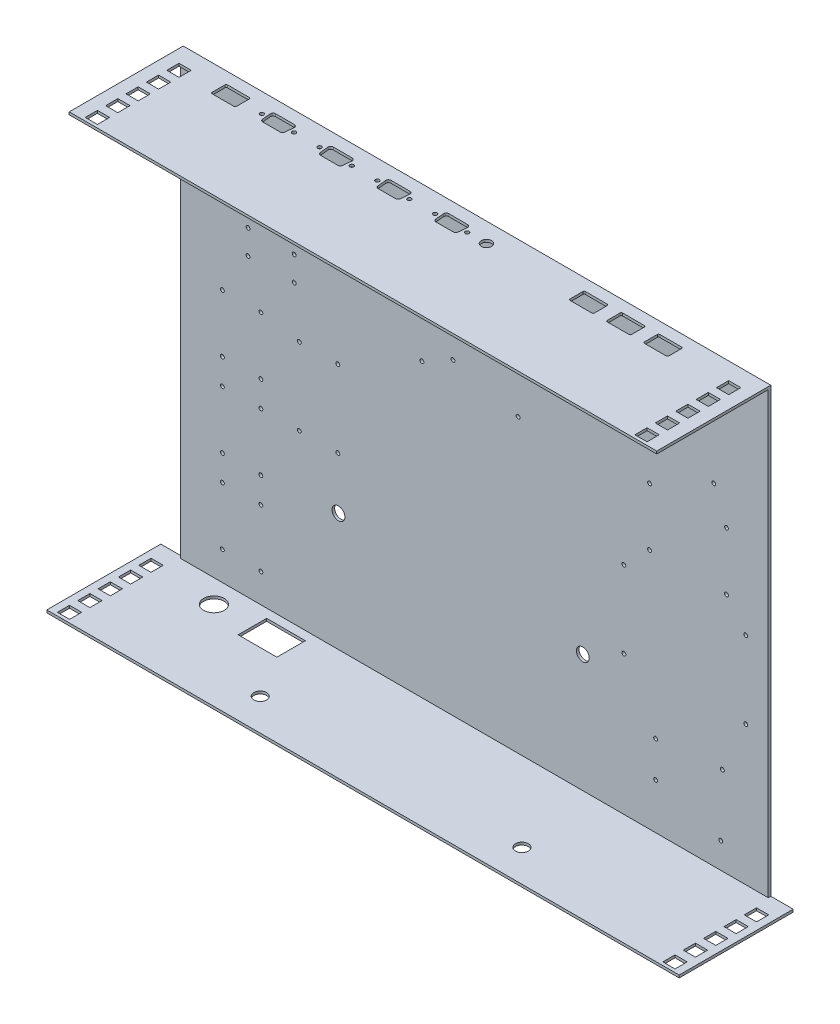
SolidWorks part; units mm, degrees
ref_plane "Front Plane" through (0, 0, 0) normal (0, 0, 1) x (1, 0, 0)
ref_plane "Top Plane" through (0, 0, 0) normal (0, 1, 0) x (1, 0, 0)
ref_plane "Right Plane" through (0, 0, 0) normal (1, 0, 0) x (0, 0, -1)
sketch "Sketch1" plane through (0, 0, 0) normal (0, 0, 1) x (1, 0, 0)
  line L13 (-229, -173.5) -> (229, -173.5)
  line L14 (-229, -173.5) -> (-229, 173.5)
  line L19 (-229, 173.5) -> (229, 173.5)
  line L20 (229, -173.5) -> (229, 173.5)
  line L21 (-229, -173.5) -> (229, 173.5) construction
  line L22 (-229, 173.5) -> (229, -173.5) construction
  point P0 (0, 0)
  dimension "D1" = 458
  dimension "D2" = 347
extrude "Boss-Extrude1" add sketch "Sketch1" along normal blind 2
sketch "Sketch4" plane through (0, -173.5, 0) normal (0, -1, 0) x (1, 0, 0)
  line L0 (-229, 2) -> (-229, 0) construction
  line L1 (-246.5, 0) -> (246.5, 0)
  line L2 (-246.5, 0) -> (-246.5, 88.9)
  line L3 (-246.5, 88.9) -> (246.5, 88.9)
  line L4 (246.5, 0) -> (246.5, 88.9)
  line L5 (229, 2) -> (229, 0) construction
  line L6 (-231.25, 88.9) -> (-231.25, 0) construction
  line L7 (-240.75, 61.02) -> (-231.25, 61.02)
  line L8 (-240.75, 86.4) -> (-231.25, 86.4)
  line L9 (-240.75, 86.4) -> (-240.75, 76.9)
  line L10 (-240.75, 76.9) -> (-231.25, 76.9)
  line L11 (-231.25, 86.4) -> (-231.25, 76.9)
  line L12 (-240.75, 70.52) -> (-240.75, 61.02)
  line L13 (-240.75, 70.52) -> (-231.25, 70.52)
  line L14 (-231.25, 70.52) -> (-231.25, 61.02)
  line L15 (-240.75, 45.14) -> (-231.25, 45.14)
  line L16 (-240.75, 54.64) -> (-240.75, 45.14)
  line L17 (-240.75, 54.64) -> (-231.25, 54.64)
  line L18 (-231.25, 54.64) -> (-231.25, 45.14)
  line L19 (-240.75, 29.26) -> (-231.25, 29.26)
  line L20 (-240.75, 38.76) -> (-240.75, 29.26)
  line L21 (-240.75, 38.76) -> (-231.25, 38.76)
  line L22 (-231.25, 38.76) -> (-231.25, 29.26)
  line L23 (-240.75, 13.38) -> (-231.25, 13.38)
  line L24 (-240.75, 22.88) -> (-240.75, 13.38)
  line L25 (-240.75, 22.88) -> (-231.25, 22.88)
  line L26 (-231.25, 22.88) -> (-231.25, 13.38)
  line L27 (0, 0) -> (0, 101.053) construction
  line L28 (231.25, 22.88) -> (231.25, 13.38)
  line L29 (240.75, 13.38) -> (231.25, 13.38)
  line L30 (240.75, 22.88) -> (240.75, 13.38)
  line L31 (240.75, 22.88) -> (231.25, 22.88)
  line L32 (231.25, 38.76) -> (231.25, 29.26)
  line L33 (240.75, 29.26) -> (231.25, 29.26)
  line L34 (240.75, 38.76) -> (240.75, 29.26)
  line L35 (240.75, 38.76) -> (231.25, 38.76)
  line L36 (240.75, 54.64) -> (240.75, 45.14)
  line L37 (231.25, 54.64) -> (231.25, 45.14)
  line L38 (240.75, 45.14) -> (231.25, 45.14)
  line L39 (240.75, 54.64) -> (231.25, 54.64)
  line L40 (231.25, 70.52) -> (231.25, 61.02)
  line L41 (240.75, 61.02) -> (231.25, 61.02)
  line L42 (240.75, 70.52) -> (231.25, 70.52)
  line L43 (240.75, 70.52) -> (240.75, 61.02)
  line L44 (231.25, 86.4) -> (231.25, 76.9)
  line L45 (240.75, 86.4) -> (231.25, 86.4)
  line L46 (240.75, 86.4) -> (240.75, 76.9)
  line L47 (240.75, 76.9) -> (231.25, 76.9)
  dimension "D1" = 17.5
  dimension "D2" = 17.5
  dimension "D3" = 88.9
  dimension "D4" = 2.25
  dimension "D5" = 9.5
  dimension "D6" = 2.5
  dimension "D7" = 9.5
  dimension "D9" = 15.88
  dimension "D8" = 5
extrude "Boss-Extrude4" add sketch "Sketch4" against normal blind 2
ref_plane "Plane1" through (0, 0, 0) normal (0, 1, 0) x (1, 0, 0)
mirror "Mirror1" about plane through (0, 0, 0) normal (0, 1, 0) of "Boss-Extrude4"
sketch "Sketch5" plane through (0, 173.5, 0) normal (0, 1, 0) x (1, 0, 0)
  line L0 (-229, 0) -> (-229, -88.9) construction
  line L1 (246.5, 0) -> (-246.5, 0) construction
  line L2 (246.5, -88.9) -> (-246.5, -88.9) construction
  line L7 (0, -55) -> (0, 55) construction
  line L11 (-229, 0) -> (-246.5, 0)
  line L12 (-229, 0) -> (-229, -88.9)
  line L13 (-229, -88.9) -> (-246.5, -88.9)
  line L14 (-246.5, 0) -> (-246.5, -88.9)
  line L15 (229, 0) -> (246.5, 0)
  line L16 (246.5, 0) -> (246.5, -88.9)
  line L17 (229, -88.9) -> (246.5, -88.9)
  line L18 (229, 0) -> (229, -88.9)
extrude "Cut-Extrude2" cut sketch "Sketch5" against normal up to next
sketch "Sketch6" plane through (0, 173.5, 0) normal (0, 1, 0) x (1, 0, 0)
  line L0 (-229, -88.9) -> (-229, 0) construction
  line L1 (-219, -13.32) -> (-209.5, -13.32)
  line L2 (-219, -13.32) -> (-219, -22.82)
  line L3 (-219, -22.82) -> (-209.5, -22.82)
  line L4 (-209.5, -13.32) -> (-209.5, -22.82)
  line L6 (-219, -29.22) -> (-219, -38.72)
  line L7 (-219, -29.22) -> (-209.5, -29.22)
  line L8 (-219, -38.72) -> (-209.5, -38.72)
  line L9 (-209.5, -29.22) -> (-209.5, -38.72)
  line L10 (-219, -45.12) -> (-219, -54.62)
  line L11 (-219, -45.12) -> (-209.5, -45.12)
  line L12 (-219, -54.62) -> (-209.5, -54.62)
  line L13 (-209.5, -45.12) -> (-209.5, -54.62)
  line L14 (-219, -61.02) -> (-219, -70.52)
  line L15 (-219, -61.02) -> (-209.5, -61.02)
  line L16 (-219, -70.52) -> (-209.5, -70.52)
  line L17 (-209.5, -61.02) -> (-209.5, -70.52)
  line L18 (-219, -76.92) -> (-219, -86.42)
  line L19 (-219, -76.92) -> (-209.5, -76.92)
  line L20 (-219, -86.42) -> (-209.5, -86.42)
  line L21 (-209.5, -76.92) -> (-209.5, -86.42)
  line L22 (0, -55) -> (0, 55) construction
  line L23 (219, -45.12) -> (209.5, -45.12)
  line L24 (219, -45.12) -> (219, -54.62)
  line L25 (209.5, -45.12) -> (209.5, -54.62)
  line L26 (219, -54.62) -> (209.5, -54.62)
  line L27 (219, -61.02) -> (209.5, -61.02)
  line L28 (209.5, -61.02) -> (209.5, -70.52)
  line L29 (219, -70.52) -> (209.5, -70.52)
  line L30 (219, -61.02) -> (219, -70.52)
  line L31 (219, -76.92) -> (219, -86.42)
  line L32 (219, -86.42) -> (209.5, -86.42)
  line L33 (209.5, -76.92) -> (209.5, -86.42)
  line L34 (219, -76.92) -> (209.5, -76.92)
  line L35 (219, -13.32) -> (219, -22.82)
  line L36 (219, -13.32) -> (209.5, -13.32)
  line L37 (209.5, -13.32) -> (209.5, -22.82)
  line L38 (219, -22.82) -> (209.5, -22.82)
  line L39 (219, -29.22) -> (219, -38.72)
  line L40 (219, -38.72) -> (209.5, -38.72)
  line L41 (209.5, -29.22) -> (209.5, -38.72)
  line L42 (219, -29.22) -> (209.5, -29.22)
  line L43 (229, -88.9) -> (-229, -88.9) construction
  dimension "D1" = 9.5
  dimension "D2" = 9.5
  dimension "D3" = 10
  dimension "D4" = 2.48
  dimension "D6" = 6.4
  dimension "D5" = 5
extrude "Cut-Extrude3" cut sketch "Sketch6" against normal up to next
sketch "Sketch9" plane through (0, 0, 2) normal (0, 0, 1) x (1, 0, 0)
  line L0 (-91, -171.5) -> (-91, 10.5) construction
  line L1 (246.5, -171.5) -> (-246.5, -171.5) construction
  line L2 (77, -171.5) -> (77, 10.5) construction
  line L3 (-229, -171.5) -> (229, -171.5) construction
  line L4 (-91, 10.5) -> (77, 10.5) construction
  line L5 (-229, 171.5) -> (-229, -171.5) construction
  circle A0 centre (-106, -79.5) radius 5
  circle A3 centre (84.5, -79.5) radius 5
  dimension "D5" = 10
  dimension "D6" = 10
  dimension "D1" = 138
  dimension "D2" = 168
  dimension "D3" = 182
  dimension "D8" = 15
  dimension "D9" = 90
  dimension "D14" = 15
  dimension "D15" = 90
extrude "Cut-Extrude4" cut sketch "Sketch9" against normal up to next
sketch "Sketch11" plane through (0, -173.5, 0) normal (0, -1, 0) x (1, 0, 0)
  line L0 (-90, 0) -> (-90, 85.1375) construction
  line L1 (-246.5, 0) -> (246.5, 0) construction
  line L2 (84, 0) -> (84, 87.0276) construction
  line L10 (-246.5, 88.9) -> (-246.5, 0) construction
  line L11 (-90, 79) -> (84, 79) construction
  circle A0 centre (-105, 64) radius 5
  circle A1 centre (99, 64) radius 5
  dimension "D4" = 10
  dimension "D5" = 10
  dimension "D1" = 174
  dimension "D2" = 156.5
  dimension "D3" = 79
  dimension "D6" = 15
  dimension "D7" = 15
  dimension "D8" = 15
  dimension "D9" = 15
extrude "Cut-Extrude5" cut sketch "Sketch11" against normal up to next
sketch "Sketch12" plane through (0, 0, 2) normal (0, 0, 1) x (1, 0, 0)
  line L0 (-229, -171.5) -> (229, -171.5) construction
  line L1 (-199, -151.5) -> (-164, -151.5)
  line L2 (-199, -151.5) -> (-199, -101.5)
  line L3 (-199, -101.5) -> (-164, -101.5)
  line L4 (-164, -151.5) -> (-164, -101.5)
  line L5 (-199, -151.5) -> (-164, -101.5) construction
  line L6 (-199, -101.5) -> (-164, -151.5) construction
  line L7 (-229, 171.5) -> (-229, -171.5) construction
  line L12 (-199, -86.5) -> (-164, -86.5)
  line L13 (-199, -86.5) -> (-199, -36.5)
  line L18 (-199, -36.5) -> (-164, -36.5)
  line L19 (-164, -86.5) -> (-164, -36.5)
  line L20 (-199, -101.5) -> (-199, 47.085) construction
  line L21 (-199, -86.5) -> (-164, -36.5) construction
  line L22 (-199, -36.5) -> (-164, -86.5) construction
  line L23 (-199, -21.5) -> (-164, -21.5)
  line L24 (-199, -21.5) -> (-199, 28.5)
  line L25 (-199, 28.5) -> (-164, 28.5)
  line L26 (-164, -21.5) -> (-164, 28.5)
  line L27 (-199, -21.5) -> (-164, 28.5) construction
  line L28 (-199, 28.5) -> (-164, -21.5) construction
  line L30 (-139, 23.5) -> (-104, 23.5)
  line L31 (-139, 23.5) -> (-139, -41.5)
  line L32 (-139, -41.5) -> (-104, -41.5)
  line L33 (-104, 23.5) -> (-104, -41.5)
  line L34 (-121.5, -41.5) -> (-121.5, 23.5) construction
  line L35 (-139, -9) -> (-104, -9) construction
  circle A0 centre (-196.5, -149) radius 1.5
  circle A1 centre (-166.5, -149) radius 1.5
  circle A2 centre (-166.5, -104) radius 1.5
  circle A3 centre (-196.5, -104) radius 1.5
  circle A12 centre (-196.5, -84) radius 1.5
  circle A13 centre (-166.5, -84) radius 1.5
  circle A14 centre (-166.5, -39) radius 1.5
  circle A15 centre (-196.5, -39) radius 1.5
  circle A16 centre (-196.5, -19) radius 1.5
  circle A17 centre (-166.5, -19) radius 1.5
  circle A18 centre (-166.5, 26) radius 1.5
  circle A19 centre (-196.5, 26) radius 1.5
  circle A20 centre (-136.5, 21) radius 1.5
  circle A21 centre (-106.5, 21) radius 1.5
  circle A22 centre (-106.5, -39) radius 1.5
  circle A23 centre (-136.5, -39) radius 1.5
  point P4 (-181.5, -126.5)
  point P21 (-181.5, -61.5)
  point P34 (-181.5, 3.5)
  point P43 (-181.5, 28.5)
  point P205 (-121.5, -9)
  dimension "D7" = 3
  dimension "D8" = 3
  dimension "D13" = 3
  dimension "D16" = 3
  dimension "D19" = 2.5
  dimension "D22" = 3
  dimension "D20" = 3
  dimension "D27" = 3
  dimension "D30" = 3
  dimension "D34" = 3
  dimension "D36" = 3
  dimension "D41" = 3
  dimension "D44" = 3
  dimension "D51" = 3
  dimension "D52" = 3
  dimension "D53" = 3
  dimension "D54" = 3
  dimension "D1" = 20
  dimension "D2" = 30
  dimension "D3" = 35
  dimension "D4" = 50
  dimension "D5" = 2.5
  dimension "D6" = 2.5
  dimension "D9" = 2.5
  dimension "D10" = 2.5
  dimension "D11" = 2.5
  dimension "D12" = 2.5
  dimension "D14" = 2.5
  dimension "D15" = 2.5
  dimension "D17" = 35
  dimension "D18" = 50
  dimension "D21" = 2.5
  dimension "D23" = 2.5
  dimension "D24" = 2.5
  dimension "D25" = 2.5
  dimension "D26" = 2.5
  dimension "D28" = 2.5
  dimension "D29" = 2.5
  dimension "D31" = 35
  dimension "D32" = 50
  dimension "D33" = 2.5
  dimension "D35" = 2.5
  dimension "D37" = 2.5
  dimension "D38" = 2.5
  dimension "D39" = 2.5
  dimension "D40" = 2.5
  dimension "D42" = 2.5
  dimension "D43" = 2.5
  dimension "D45" = 15
  dimension "D46" = 15
  dimension "D47" = 35
  dimension "D48" = 65
  dimension "D49" = 25
  dimension "D50" = 5
  dimension "D55" = 2.5
  dimension "D56" = 2.5
  dimension "D57" = 2.5
  dimension "D58" = 2.5
  dimension "D59" = 2.5
  dimension "D60" = 2.5
  dimension "D61" = 2.5
  dimension "D62" = 2.5
extrude "Cut-Extrude6" cut sketch "Sketch12" against normal blind 30 contours A0 | A1 | A12 | A13 | A15 | A14 | A16 | A3 | A2 | A17 | A23 | A22 | A20 | A21 | A18 | A19
sketch "Sketch15" plane through (0, 0, 2) normal (0, 0, 1) x (1, 0, 0)
  line L0 (35.28, 104.261) -> (-47.198, 104.261) construction
  line L1 (-179, 56.5) -> (-138, 56.5)
  line L2 (-179, 56.5) -> (-179, 80.5)
  line L3 (-179, 80.5) -> (-138, 80.5)
  line L4 (-138, 56.5) -> (-138, 80.5)
  line L5 (-158.5, 80.5) -> (-158.5, 56.5) construction
  line L6 (-179, 68.5) -> (-138, 68.5) construction
  line L7 (-64, 116.5) -> (56, 116.5)
  line L8 (-64, 116.5) -> (-64, 43.5)
  line L9 (-64, 43.5) -> (56, 43.5)
  line L10 (56, 116.5) -> (56, 43.5)
  line L11 (-4, 43.5) -> (-4, 116.5) construction
  line L12 (-64, 80) -> (56, 80) construction
  line L13 (94, 136.5) -> (189, 136.5)
  line L14 (94, 136.5) -> (94, 84.5)
  line L15 (94, 84.5) -> (189, 84.5)
  line L16 (189, 136.5) -> (189, 84.5)
  line L17 (141.5, 84.5) -> (141.5, 136.5) construction
  line L18 (94, 110.5) -> (189, 110.5) construction
  line L19 (134, 64.5) -> (199, 64.5)
  line L20 (134, 64.5) -> (134, 14.5)
  line L21 (134, 14.5) -> (199, 14.5)
  line L22 (199, 64.5) -> (199, 14.5)
  line L23 (166.5, 14.5) -> (166.5, 64.5) construction
  line L24 (134, 39.5) -> (199, 39.5) construction
  line L25 (114, -0.5) -> (214, -0.5)
  line L26 (114, -0.5) -> (114, -65.5)
  line L27 (114, -65.5) -> (214, -65.5)
  line L28 (214, -0.5) -> (214, -65.5)
  line L29 (164, -65.5) -> (164, -0.5) construction
  line L30 (114, -33) -> (214, -33) construction
  line L31 (138.725, -90.5) -> (214, -90.5)
  line L32 (138.725, -90.5) -> (138.725, -163.5)
  line L33 (138.725, -163.5) -> (214, -163.5)
  line L34 (214, -90.5) -> (214, -163.5)
  line L35 (176.3625, -163.5) -> (176.3625, -90.5) construction
  line L36 (138.725, -127) -> (214, -127) construction
  line L41 (-229, 171.5) -> (-229, -171.5) construction
  line L42 (229, 171.5) -> (-229, 171.5) construction
  line L43 (229, -171.5) -> (229, 171.5) construction
  line L44 (96.5, 87) -> (186.5, 87)
  line L45 (-176.5, 59) -> (-140.5, 59)
  line L46 (-176.5, 59) -> (-176.5, 78)
  line L47 (-176.5, 78) -> (-140.5, 78)
  line L48 (-140.5, 59) -> (-140.5, 78)
  line L49 (-176.5, 59) -> (-140.5, 78) construction
  line L50 (-176.5, 78) -> (-140.5, 59) construction
  line L51 (96.5, 87) -> (96.5, 134)
  line L52 (96.5, 134) -> (186.5, 134)
  line L53 (186.5, 87) -> (186.5, 134)
  line L54 (96.5, 87) -> (186.5, 134) construction
  line L55 (96.5, 134) -> (186.5, 87) construction
  line L56 (136.5, 17) -> (196.5, 17)
  line L57 (136.5, 17) -> (136.5, 62)
  line L58 (136.5, 62) -> (196.5, 62)
  line L59 (196.5, 17) -> (196.5, 62)
  line L60 (136.5, 17) -> (196.5, 62) construction
  line L61 (136.5, 62) -> (196.5, 17) construction
  line L62 (116.5, -63) -> (211.5, -63)
  line L63 (116.5, -63) -> (116.5, -3)
  line L64 (116.5, -3) -> (211.5, -3)
  line L65 (211.5, -63) -> (211.5, -3)
  line L66 (116.5, -63) -> (211.5, -3) construction
  line L67 (116.5, -3) -> (211.5, -63) construction
  line L68 (-52.35, 53.2) -> (56, 53.2)
  line L69 (-52.35, 53.2) -> (-52.35, 106.8)
  line L70 (-52.35, 106.8) -> (56, 106.8)
  line L71 (56, 53.2) -> (56, 106.8)
  line L72 (1.825, 106.8) -> (1.825, 53.2) construction
  line L73 (-52.35, 80) -> (56, 80) construction
  line L74 (-16.75, 104.261) -> (-16.75, 53.2) construction
  line L75 (141.25, -100.35) -> (141.25, -153.65) construction
  line L76 (138.72, -153.65) -> (214, -153.65)
  line L77 (138.72, -153.65) -> (138.72, -100.35)
  line L78 (138.72, -100.35) -> (214, -100.35)
  line L79 (214, -153.65) -> (214, -100.35)
  line L80 (176.36, -100.35) -> (176.36, -153.65) construction
  line L81 (138.72, -127) -> (214, -127) construction
  circle A0 centre (-176.5, 78) radius 1.4993
  circle A1 centre (-176.5, 59) radius 1.5
  circle A2 centre (-140.5, 59) radius 1.5
  circle A3 centre (-140.5, 78) radius 1.5
  circle A4 centre (116.5, -3) radius 1.5
  circle A5 centre (116.5, -63) radius 1.5
  circle A6 centre (211.5, -63) radius 1.5
  circle A7 centre (211.5, -3) radius 1.5
  circle A8 centre (136.5, 62) radius 1.5
  circle A9 centre (136.5, 17) radius 1.5
  circle A10 centre (196.5, 17) radius 1.5
  circle A11 centre (196.5, 62) radius 1.5
  circle A12 centre (96.5, 134) radius 1.5
  circle A13 centre (96.5, 87) radius 1.5
  circle A14 centre (186.5, 87) radius 1.5
  circle A15 centre (186.5, 134) radius 1.5
  circle A16 centre (35.28, 104.261) radius 1.5
  circle A17 centre (-47.198, 104.261) radius 1.5
  circle A18 centre (-40.945, 55.739) radius 1.5
  circle A19 centre (34.01, 55.739) radius 1.5
  circle A20 centre (-16.75, 96.644) radius 1.5
  circle A21 centre (-16.75, 68.735) radius 1.5
  circle A22 centre (193.28, -102.889) radius 1.5
  circle A23 centre (192.015, -151.411) radius 1.5
  circle A24 centre (141.25, -107.967) radius 1.5
  circle A25 centre (141.25, -135.876) radius 1.5
  point P30 (-158.5, 68.5)
  point P39 (141.5, 110.5)
  point P44 (166.5, 39.5)
  point P49 (164, -33)
  point P124 (176.3625, -127)
  point P152 (-4, 80)
  point P164 (-158.5, 68.5)
  point P194 (164, -33)
  point P246 (141.5, 110.5)
  point P275 (166.5, 39.5)
  point P395 (176.36, -127)
  point P605 (1.825, 80)
  dimension "D27" = 2.9987
  dimension "D28" = 3
  dimension "D29" = 3
  dimension "D30" = 3
  dimension "D33" = 3
  dimension "D34" = 3
  dimension "D35" = 3
  dimension "D36" = 3
  dimension "D39" = 3
  dimension "D40" = 3
  dimension "D41" = 3
  dimension "D42" = 3
  dimension "D45" = 3
  dimension "D46" = 3
  dimension "D47" = 3
  dimension "D48" = 3
  dimension "D52" = 3
  dimension "D57" = 3
  dimension "D58" = 3
  dimension "D59" = 3
  dimension "D66" = 3
  dimension "D67" = 3
  dimension "D71" = 3
  dimension "D72" = 3
  dimension "D78" = 3
  dimension "D79" = 3
  dimension "D1" = 50
  dimension "D2" = 115
  dimension "D3" = 24
  dimension "D4" = 41
  dimension "D5" = 73
  dimension "D6" = 120
  dimension "D7" = 73
  dimension "D8" = 75.275
  dimension "D9" = 52
  dimension "D10" = 95
  dimension "D11" = 50
  dimension "D12" = 65
  dimension "D13" = 65
  dimension "D14" = 100
  dimension "D15" = 55
  dimension "D16" = 165
  dimension "D17" = 35
  dimension "D18" = 40
  dimension "D19" = 20
  dimension "D20" = 30
  dimension "D21" = 15
  dimension "D22" = 15
  dimension "D23" = 15
  dimension "D24" = 25
  dimension "D25" = 2.5
  dimension "D26" = 2.5
  dimension "D31" = 2.5
  dimension "D32" = 2.5
  dimension "D37" = 2.5
  dimension "D38" = 2.5
  dimension "D43" = 2.5
  dimension "D44" = 2.5
  dimension "D49" = 53.6
  dimension "D50" = 108.35
  dimension "D51" = 0
  dimension "D53" = 2.539
  dimension "D54" = 20.72
  dimension "D55" = 82.478
  dimension "D56" = 48.522
  dimension "D60" = 48.522
  dimension "D61" = 21.99
  dimension "D62" = 11.405
  dimension "D63" = 52.03
  dimension "D64" = 7.617
  dimension "D65" = 27.909
  dimension "D68" = 75.28
  dimension "D69" = 53.3
  dimension "D70" = 0
  dimension "D73" = 20.72
  dimension "D74" = 2.539
  dimension "D75" = 21.985
  dimension "D76" = 48.522
  dimension "D77" = 52.03
  dimension "D80" = 27.909
  dimension "D81" = 7.617
extrude "Cut-Extrude7" cut sketch "Sketch15" against normal up to next (2 mm away) contours A2 | A1 | A0 | A3 | A17 | A18 | A21 | A20 | A19 | A16 | A12 | A13 | A14 | A15 | A9 | A8 | A11 | A10 | A4 | A5 | A7 | A6 | A25 | A24 | A22 | A23
sketch "Sketch16" plane through (0, 173.5, 0) normal (0, 1, 0) x (1, 0, 0)
  line L0 (-195.0235, -15) -> (195.2186, -15) construction
  line L2 (-147.3524, -9.7) -> (-132.6476, -9.7)
  line L4 (-140, -28.7384) -> (-140, -16.1884) construction
  line L5 (-146.7298, -20.3) -> (-133.2702, -20.3)
  line L8 (-130.45, -9.7) -> (-130.45, -26.4134) construction
  line L9 (229, 0) -> (-229, 0) construction
  line L10 (-102.3524, -9.7) -> (-87.6476, -9.7)
  line L23 (-149.55, -9.7) -> (-149.55, -23.1825) construction
  line L25 (-130.6564, -11.8878) -> (-131.279, -18.4878)
  line L27 (-149.3436, -11.8878) -> (-148.721, -18.4878)
  line L28 (-149.55, -9.7) -> (-149.55, -9.1639) construction
  line L29 (-85.6564, -11.8878) -> (-86.279, -18.4878)
  line L30 (-101.7298, -20.3) -> (-88.2702, -20.3)
  line L31 (-104.3436, -11.8878) -> (-103.721, -18.4878)
  line L32 (-57.3524, -9.7) -> (-42.6476, -9.7)
  line L33 (-40.6564, -11.8878) -> (-41.279, -18.4878)
  line L34 (-56.7298, -20.3) -> (-43.2702, -20.3)
  line L35 (-59.3436, -11.8878) -> (-58.721, -18.4878)
  line L36 (-12.3524, -9.7) -> (2.3524, -9.7)
  line L37 (4.3436, -11.8878) -> (3.721, -18.4878)
  line L38 (-11.7298, -20.3) -> (1.7298, -20.3)
  line L39 (-14.3436, -11.8878) -> (-13.721, -18.4878)
  line L40 (-185.5023, -21) -> (-168.5023, -21)
  line L41 (-186.5023, -20) -> (-186.5023, -10)
  line L42 (-185.5023, -9) -> (-168.5023, -9)
  line L43 (-167.5023, -20) -> (-167.5023, -10)
  line L44 (-186.5023, -21) -> (-167.5023, -9) construction
  line L45 (-186.5023, -9) -> (-167.5023, -21) construction
  line L46 (122.5023, -21) -> (139.5023, -21)
  line L47 (121.5023, -20) -> (121.5023, -10)
  line L48 (122.5023, -9) -> (139.5023, -9)
  line L49 (140.5023, -20) -> (140.5023, -10)
  line L50 (121.5023, -21) -> (140.5023, -9) construction
  line L51 (121.5023, -9) -> (140.5023, -21) construction
  line L52 (151.5023, -21) -> (168.5023, -21)
  line L53 (150.5023, -20) -> (150.5023, -10)
  line L54 (151.5023, -9) -> (168.5023, -9)
  line L55 (169.5023, -20) -> (169.5023, -10)
  line L56 (150.5023, -21) -> (169.5023, -9) construction
  line L57 (150.5023, -9) -> (169.5023, -21) construction
  line L58 (93.5023, -21) -> (110.5023, -21)
  line L59 (92.5023, -20) -> (92.5023, -10)
  line L60 (93.5023, -9) -> (110.5023, -9)
  line L61 (111.5023, -20) -> (111.5023, -10)
  line L62 (92.5023, -21) -> (111.5023, -9) construction
  line L63 (92.5023, -9) -> (111.5023, -21) construction
  arc A31 (-131.279, -18.4878) -> (-133.2702, -20.3) centre (-133.2702, -18.3) cw
  arc A32 (-146.7298, -20.3) -> (-148.721, -18.4878) centre (-146.7298, -18.3) cw
  arc A33 (-130.6564, -11.8878) -> (-132.6476, -9.7) centre (-132.6476, -11.7) ccw
  arc A34 (-149.3436, -11.8878) -> (-147.3524, -9.7) centre (-147.3524, -11.7) cw
  circle A35 centre (-152.5023, -15.1878) radius 1.5
  circle A36 centre (-127.4977, -15.1878) radius 1.5
  arc A37 (-85.6564, -11.8878) -> (-87.6476, -9.7) centre (-87.6476, -11.7) ccw
  arc A38 (-86.279, -18.4878) -> (-88.2702, -20.3) centre (-88.2702, -18.3) cw
  arc A39 (-101.7298, -20.3) -> (-103.721, -18.4878) centre (-101.7298, -18.3) cw
  arc A40 (-104.3436, -11.8878) -> (-102.3524, -9.7) centre (-102.3524, -11.7) cw
  circle A41 centre (-107.5023, -15.1878) radius 1.5
  circle A42 centre (-82.4977, -15.1878) radius 1.5
  arc A43 (-40.6564, -11.8878) -> (-42.6476, -9.7) centre (-42.6476, -11.7) ccw
  arc A44 (-41.279, -18.4878) -> (-43.2702, -20.3) centre (-43.2702, -18.3) cw
  arc A45 (-56.7298, -20.3) -> (-58.721, -18.4878) centre (-56.7298, -18.3) cw
  arc A46 (-59.3436, -11.8878) -> (-57.3524, -9.7) centre (-57.3524, -11.7) cw
  circle A47 centre (-62.5023, -15.1878) radius 1.5
  circle A48 centre (-37.4977, -15.1878) radius 1.5
  arc A49 (4.3436, -11.8878) -> (2.3524, -9.7) centre (2.3524, -11.7) ccw
  arc A50 (3.721, -18.4878) -> (1.7298, -20.3) centre (1.7298, -18.3) cw
  arc A51 (-11.7298, -20.3) -> (-13.721, -18.4878) centre (-11.7298, -18.3) cw
  arc A52 (-14.3436, -11.8878) -> (-12.3524, -9.7) centre (-12.3524, -11.7) cw
  circle A53 centre (-17.5023, -15.1878) radius 1.5
  circle A54 centre (7.5023, -15.1878) radius 1.5
  circle A55 centre (22.5023, -15.1878) radius 4
  arc A56 (-185.5023, -21) -> (-186.5023, -20) centre (-185.5023, -20) cw
  arc A57 (-168.5023, -21) -> (-167.5023, -20) centre (-168.5023, -20) ccw
  arc A58 (-168.5023, -9) -> (-167.5023, -10) centre (-168.5023, -10) cw
  arc A59 (-186.5023, -10) -> (-185.5023, -9) centre (-185.5023, -10) cw
  arc A60 (122.5023, -21) -> (121.5023, -20) centre (122.5023, -20) cw
  arc A61 (139.5023, -21) -> (140.5023, -20) centre (139.5023, -20) ccw
  arc A62 (139.5023, -9) -> (140.5023, -10) centre (139.5023, -10) cw
  arc A63 (121.5023, -10) -> (122.5023, -9) centre (122.5023, -10) cw
  arc A64 (151.5023, -21) -> (150.5023, -20) centre (151.5023, -20) cw
  arc A65 (168.5023, -21) -> (169.5023, -20) centre (168.5023, -20) ccw
  arc A66 (168.5023, -9) -> (169.5023, -10) centre (168.5023, -10) cw
  arc A67 (150.5023, -10) -> (151.5023, -9) centre (151.5023, -10) cw
  arc A68 (93.5023, -21) -> (92.5023, -20) centre (93.5023, -20) cw
  arc A69 (110.5023, -21) -> (111.5023, -20) centre (110.5023, -20) ccw
  arc A70 (110.5023, -9) -> (111.5023, -10) centre (110.5023, -10) cw
  arc A71 (92.5023, -10) -> (93.5023, -9) centre (93.5023, -10) cw
  point P6 (-140, -9.7)
  point P10 (-149.0323, -15.1878)
  point P12 (-130.9677, -15.1878)
  point P30 (-177.0023, -15)
  point P103 (131.0023, -15)
  point P120 (160.0023, -15)
  point P137 (102.0023, -15)
  dimension "D5" = 2
  dimension "D8" = 7.3524
  dimension "D9" = 3
  dimension "D13" = 0.1878
  dimension "D16" = 8
  dimension "D22" = 19
  dimension "D10" = 3
  dimension "D20" = 1
  dimension "D24" = 1
  dimension "D27" = 1
  dimension "D30" = 1
  dimension "D1" = 5.3
  dimension "D2" = 19.1
  dimension "D3" = 5.3
  dimension "D4" = 5.389
  dimension "D6" = 15
  dimension "D7" = 140
  dimension "D11" = 3.47
  dimension "D12" = 3.47
  dimension "D15" = 19.9954
  dimension "D17" = 15
  dimension "D18" = 19
  dimension "D19" = 12
  dimension "D21" = 15
  dimension "D14" = 0.1878
  dimension "D23" = 12
  dimension "D25" = 19
  dimension "D26" = 12
  dimension "D28" = 19
  dimension "D29" = 12
  dimension "D31" = 10
  dimension "D32" = 10
  dimension "D33" = 70
extrude "Cut-Extrude9" cut sketch "Sketch16" against normal up to next
sketch "Sketch17" plane through (0, -173.5, 0) normal (0, -1, 0) x (1, 0, 0)
  line L0 (-246.5, 0) -> (246.5, 0) construction
  line L1 (-155.1, 31.1) -> (-124.9, 31.1)
  line L2 (-155.1, 31.1) -> (-155.1, 8.9)
  line L3 (-155.1, 8.9) -> (-124.9, 8.9)
  line L4 (-124.9, 31.1) -> (-124.9, 8.9)
  line L5 (-155.1, 31.1) -> (-124.9, 8.9) construction
  line L6 (-155.1, 8.9) -> (-124.9, 31.1) construction
  circle A0 centre (-185.1, 20) radius 8.05
  point P0 (-140, 20)
  dimension "D5" = 16.1
  dimension "D1" = 22.2
  dimension "D2" = 30.2
  dimension "D3" = 140
  dimension "D4" = 20
  dimension "D6" = 30
extrude "Cut-Extrude10" cut sketch "Sketch17" against normal up to next
